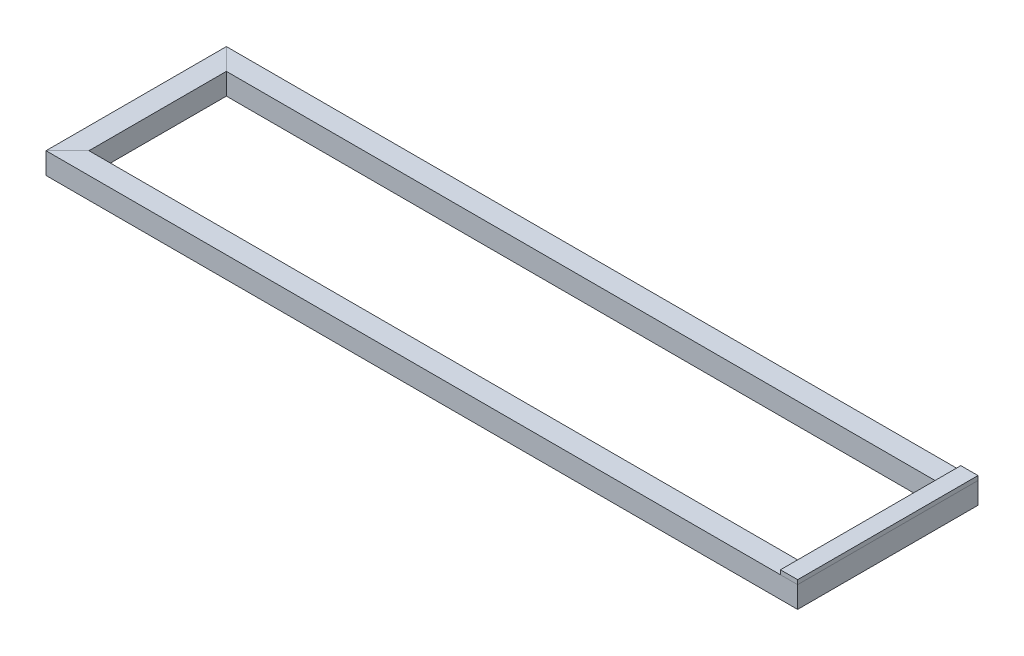
SolidWorks part; units mm, degrees
ref_plane "前视基准面" through (0, 0, 0) normal (0, 0, 1) x (1, 0, 0)
ref_plane "上视基准面" through (0, 0, 0) normal (0, 1, 0) x (1, 0, 0)
ref_plane "右视基准面" through (0, 0, 0) normal (1, 0, 0) x (0, 0, -1)
sketch3d "3D草图1"
  line L1 (-850, 0, -185) -> (850, 0, -185)
  line L2 (-850, 0, -185) -> (-850, 0, 185)
  line L3 (-850, 0, 185) -> (850, 0, 185)
  line L4 (850, 0, -185) -> (850, 0, 185)
  line L5 (-850, 0, -185) -> (850, 0, 185) construction
  line L6 (-850, 0, 185) -> (850, 0, -185) construction
  point P0 (0, 0, 0)
  dimension "D1" = 1700
  dimension "D2" = 370
other "Square bar SQUARE BAR 50(1)"
ref_plane "基准面1" through (-850, 0, -185) normal (0, 0, 1) x (1, 0, 0)
sketch "Sketch17" plane through (-850, 0, -185) normal (0, 0, 1) x (1, 0, 0)
  line L1 (25, -25) -> (25, 25)
  line L2 (25, 25) -> (-25, 25)
  line L3 (-25, 25) -> (-25, -25)
  line L4 (-25, -25) -> (25, -25)
  circle A0 centre (0, 0) radius 25 construction
  point P1 (0, 25)
  point P7 (0, 0)
  point P8 (0, -25)
  point P9 (-25, 0)
  point P10 (25, 0)
  point P11 (0, 0)
  dimension "d" = 50
ref_plane "基准面4" through (0, 20, 0) normal (0, 1, 0) x (1, 0, 0)
sketch "草图13" plane through (0, 25, 0) normal (0, 1, 0) x (1, 0, 0)
  line L0 (875, -210) -> (-875, -210) construction
  line L1 (875, 210) -> (835, 210)
  line L2 (875, 210) -> (875, -210)
  line L3 (875, -210) -> (835, -210)
  line L4 (835, 210) -> (835, -210)
  dimension "D1" = 40
extrude "凸台-拉伸2" add sketch "草图13" along normal blind 10 separate body
